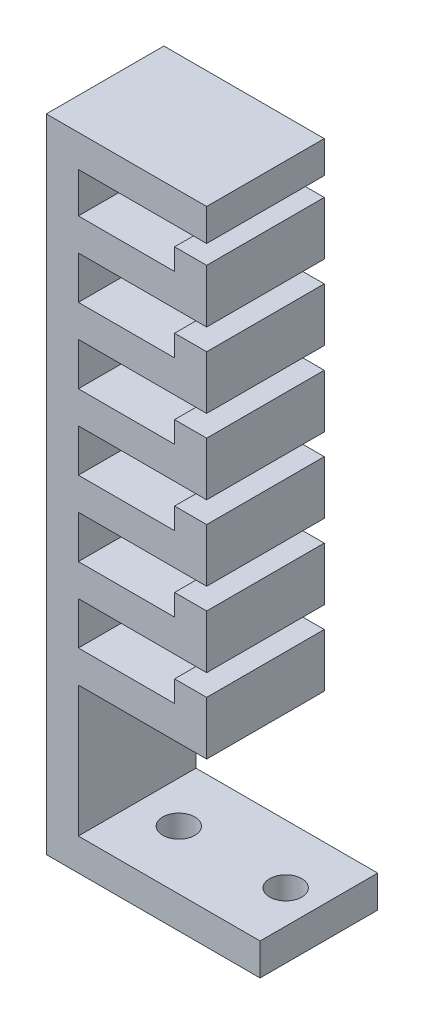
SolidWorks part; units mm, degrees
ref_plane "Front Plane" through (0, 0, 0) normal (0, 0, 1) x (1, 0, 0)
ref_plane "Top Plane" through (0, 0, 0) normal (0, 1, 0) x (1, 0, 0)
ref_plane "Right Plane" through (0, 0, 0) normal (1, 0, 0) x (0, 0, -1)
sketch "Sketch1" plane through (0, 0, 0) normal (0, 0, 1) x (1, 0, 0)
  line L0 (0, 0) -> (-20, 0)
  line L1 (-20, 0) -> (-20, 60)
  line L2 (0, 0) -> (0, 3)
  line L3 (0, 3) -> (-17, 3)
  line L5 (-17, 36.2329) -> (-5, 36.2329)
  line L6 (-5, 36.2329) -> (-5, 41.2329)
  line L7 (-5, 41.2329) -> (-8, 41.2329)
  line L8 (-8, 41.2329) -> (-8, 39.2329)
  line L9 (-8, 39.2329) -> (-17, 39.2329)
  line L18 (-17, 39.2329) -> (-17, 43.2329)
  line L22 (-20, 60) -> (-17, 60)
  line L24 (-17, 43.2329) -> (-5, 43.2329)
  line L25 (-5, 43.2329) -> (-5, 48.2329)
  line L26 (-5, 48.2329) -> (-8, 48.2329)
  line L27 (-8, 48.2329) -> (-8, 46.2329)
  line L28 (-8, 46.2329) -> (-17, 46.2329)
  line L29 (-17, 50.2329) -> (-5, 50.2329)
  line L30 (-5, 50.2329) -> (-5, 55.2329)
  line L31 (-5, 55.2329) -> (-8, 55.2329)
  line L32 (-8, 55.2329) -> (-8, 53.2329)
  line L33 (-8, 53.2329) -> (-17, 53.2329)
  line L34 (-17, 36.2329) -> (-17, 43.2329) construction
  line L35 (-17, 60) -> (-5, 60)
  line L38 (-17, 57) -> (-17, 53.2329)
  line L39 (-17, 50.2329) -> (-17, 46.2329)
  line L40 (-17, 57) -> (-5, 57)
  line L41 (-5, 57) -> (-5, 60)
  line L42 (-17, 29.2329) -> (-5, 29.2329)
  line L43 (-5, 29.2329) -> (-5, 34.2329)
  line L44 (-5, 34.2329) -> (-8, 34.2329)
  line L45 (-8, 34.2329) -> (-8, 32.2329)
  line L46 (-8, 32.2329) -> (-17, 32.2329)
  line L47 (-17, 22.2329) -> (-5, 22.2329)
  line L48 (-5, 22.2329) -> (-5, 27.2329)
  line L49 (-5, 27.2329) -> (-8, 27.2329)
  line L50 (-8, 27.2329) -> (-8, 25.2329)
  line L51 (-8, 25.2329) -> (-17, 25.2329)
  line L52 (-17, 15.2329) -> (-5, 15.2329)
  line L53 (-5, 15.2329) -> (-5, 20.2329)
  line L54 (-5, 20.2329) -> (-8, 20.2329)
  line L55 (-8, 20.2329) -> (-8, 18.2329)
  line L56 (-8, 18.2329) -> (-17, 18.2329)
  line L57 (-17, 36.2329) -> (-17, 32.2329)
  line L58 (-17, 29.2329) -> (-17, 25.2329)
  line L59 (-17, 22.2329) -> (-17, 18.2329)
  line L60 (-17, 15.2329) -> (-17, 3)
  point P3 (0, 1.5)
  dimension "D1" = 60
  dimension "D2" = 20
  dimension "D3" = 3
  dimension "D5" = 4
  dimension "D6" = 5
  dimension "D8" = 3
  dimension "D10" = 7
  dimension "D9" = 3
extrude "Boss-Extrude2" add sketch "Sketch1" along normal blind 11
sketch "Sketch4" plane through (0, 0, 0) normal (0, -1, 0) x (1, 0, 0)
  line L0 (-20, 11) -> (0, 11) construction
  circle A0 centre (-3.1033, 5.5) radius 1.5
  circle A2 centre (-13.1033, 5.5) radius 1.5
  dimension "D2" = 3
  dimension "D1" = 5.5
  dimension "D3" = 10
extrude "Cut-Extrude1" cut sketch "Sketch4" against normal blind 11
